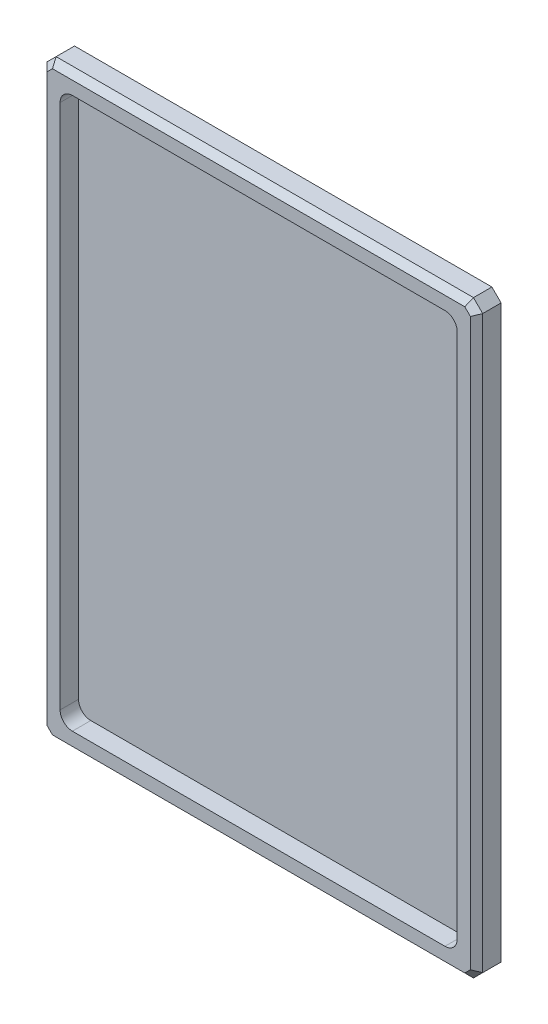
SolidWorks part; units mm, degrees
material "AISI 304"
ref_plane "Front Plane" through (0, 0, 0) normal (0, 0, 1) x (1, 0, 0)
ref_plane "Top Plane" through (0, 0, 0) normal (0, 1, 0) x (1, 0, 0)
ref_plane "Right Plane" through (0, 0, 0) normal (1, 0, 0) x (0, 0, -1)
sketch "Sketch1" plane through (0, 0, 0) normal (0, 0, 1) x (1, 0, 0)
  line L1 (112.7125, -152.4) -> (-112.7125, -152.4)
  line L2 (112.7125, -152.4) -> (112.7125, 152.4)
  line L3 (112.7125, 152.4) -> (-112.7125, 152.4)
  line L4 (-112.7125, -152.4) -> (-112.7125, 152.4)
  line L5 (112.7125, -152.4) -> (-112.7125, 152.4) construction
  line L6 (112.7125, 152.4) -> (-112.7125, -152.4) construction
  point P0 (0, 0)
  dimension "D1" = 304.8
  dimension "D2" = 225.425
extrude "Boss-Extrude1" add sketch "Sketch1" along normal blind 12.7
sketch "Sketch2" plane through (0, 0, 12.7) normal (0, 0, 1) x (1, 0, 0)
  line L0 (-112.7125, 152.4) -> (-112.7125, -152.4) construction
  line L1 (96.3625, -142.4) -> (-96.3625, -142.4)
  line L2 (102.7125, -136.05) -> (102.7125, 136.05)
  line L3 (96.3625, 142.4) -> (-96.3625, 142.4)
  line L4 (-102.7125, -136.05) -> (-102.7125, 136.05)
  line L5 (102.7125, -142.4) -> (-102.7125, 142.4) construction
  line L6 (102.7125, 142.4) -> (-102.7125, -142.4) construction
  line L7 (112.7125, 152.4) -> (-112.7125, 152.4) construction
  arc A0 (-96.3625, -142.4) -> (-102.7125, -136.05) centre (-96.3625, -136.05) cw
  arc A1 (96.3625, -142.4) -> (102.7125, -136.05) centre (96.3625, -136.05) ccw
  arc A2 (102.7125, 136.05) -> (96.3625, 142.4) centre (96.3625, 136.05) ccw
  arc A3 (-96.3625, 142.4) -> (-102.7125, 136.05) centre (-96.3625, 136.05) ccw
  point P0 (0, 0)
  dimension "D3" = 6.35
  dimension "D1" = 10
  dimension "D2" = 10
extrude "Cut-Extrude1" cut sketch "Sketch2" against normal blind 9.525
chamfer "Chamfer2" distance 4.7625 angle 45 4 edges at (-112.7125, -152.4, 6.35) (-112.7125, 152.4, 6.35) (112.7125, -152.4, 6.35) (112.7125, 152.4, 6.35)
chamfer "Chamfer1" distance 3.175 angle 45 8 edges at (0, -152.4, 12.7) (-112.7125, 0, 12.7) (112.7125, 0, 12.7) (0, 152.4, 12.7) (-110.3313, -150.0188, 12.7) (110.3313, -150.0188, 12.7) (-110.3312, 150.0187, 12.7) (110.3313, 150.0187, 12.7)
